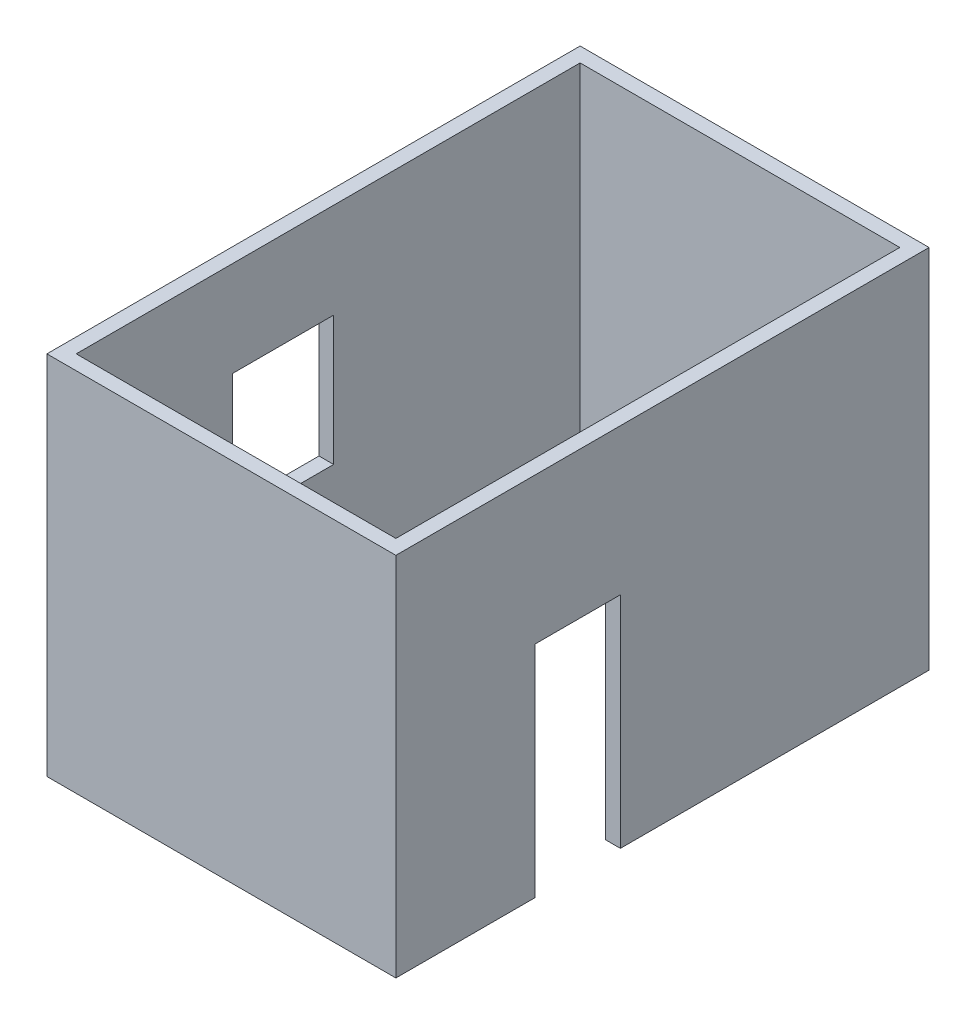
SolidWorks part; units mm, degrees
material "砖"
ref_plane "前视基准面" through (0, 0, 0) normal (0, 0, 1) x (1, 0, 0)
ref_plane "上视基准面" through (0, 0, 0) normal (0, 1, 0) x (1, 0, 0)
ref_plane "右视基准面" through (0, 0, 0) normal (1, 0, 0) x (0, 0, -1)
sketch "草图1" plane through (0, 0, 0) normal (0, 1, 0) x (1, 0, 0)
  line L1 (0, 0) -> (-2620, 0)
  line L2 (0, 0) -> (0, 4130)
  line L3 (0, 4130) -> (-2620, 4130)
  line L4 (-2620, 0) -> (-2620, 4130)
  dimension "D1" = 2620
  dimension "D2" = 4130
extrude "拉伸-薄壁1" add sketch "草图1" along normal blind 3000 thin thin type one direction wall 120
sketch "草图2" plane through (120, 0, 0) normal (1, 0, 0) x (0, 0, -1)
  line L0 (-120, 0) -> (4250, 0) construction
  line L1 (1020, 0) -> (1720, 0)
  line L2 (1020, 0) -> (1020, 1800)
  line L3 (1020, 1800) -> (1720, 1800)
  line L4 (1720, 0) -> (1720, 1800)
  dimension "D1" = 700
  dimension "D2" = 1800
  dimension "D3" = 1020
extrude "切除-拉伸1" cut sketch "草图2" against normal up to next
sketch "草图3" plane through (-2620, 0, 0) normal (1, 0, 0) x (0, 0, -1)
  line L0 (4130, 0) -> (0, 0) construction
  line L1 (1280, 2220) -> (2110, 2220)
  line L2 (1280, 2220) -> (1280, 1160)
  line L3 (1280, 1160) -> (2110, 1160)
  line L4 (2110, 2220) -> (2110, 1160)
  line L5 (4130, 3000) -> (4130, 0) construction
  dimension "D1" = 830
  dimension "D2" = 1060
  dimension "D3" = 1160
  dimension "D4" = 2020
extrude "切除-拉伸2" cut sketch "草图3" against normal up to next
